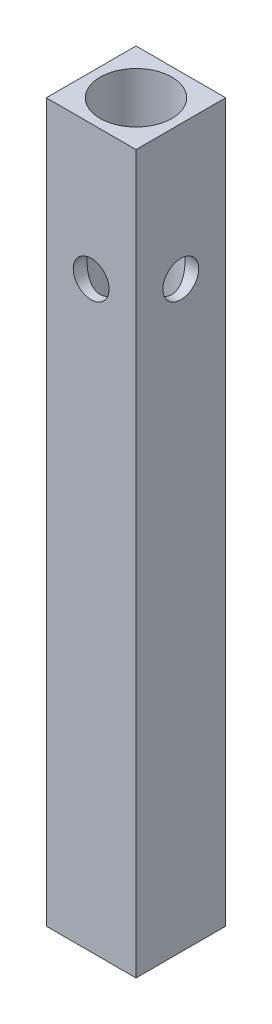
SolidWorks part; units mm, degrees
ref_plane "前视基准面" through (0, 0, 0) normal (0, 0, 1) x (1, 0, 0)
ref_plane "上视基准面" through (0, 0, 0) normal (0, 1, 0) x (1, 0, 0)
ref_plane "右视基准面" through (0, 0, 0) normal (1, 0, 0) x (0, 0, -1)
sketch "草图1" plane through (0, 0, 0) normal (0, 1, 0) x (1, 0, 0)
  line L1 (-5, 5) -> (5, 5)
  line L2 (-5, 5) -> (-5, -5)
  line L3 (-5, -5) -> (5, -5)
  line L4 (5, 5) -> (5, -5)
  dimension "D1" = 10
  dimension "D2" = 10
  dimension "D3" = 5
  dimension "D4" = 5
extrude "凸台-拉伸1" add sketch "草图1" along normal blind 80
sketch "草图4" plane through (0, 80, 0) normal (0, 1, 0) x (1, 0, 0)
  circle A0 centre (0, 0) radius 4
extrude "切除-拉伸3" cut sketch "草图4" against normal blind 75
sketch "草图5" plane through (5, 0, 0) normal (1, 0, 0) x (0, 0, -1)
  line L0 (0, 80) -> (0, 68.914) construction
  line L1 (-5, 80) -> (5, 80) construction
  circle A0 centre (0, 65) radius 2
extrude "切除-拉伸4" cut sketch "草图5" against normal through all
sketch "草图6" plane through (0, 0, -5) normal (0, 0, -1) x (-1, 0, 0)
  circle A0 centre (0, 65) radius 2
extrude "切除-拉伸5" cut sketch "草图6" against normal blind 10
